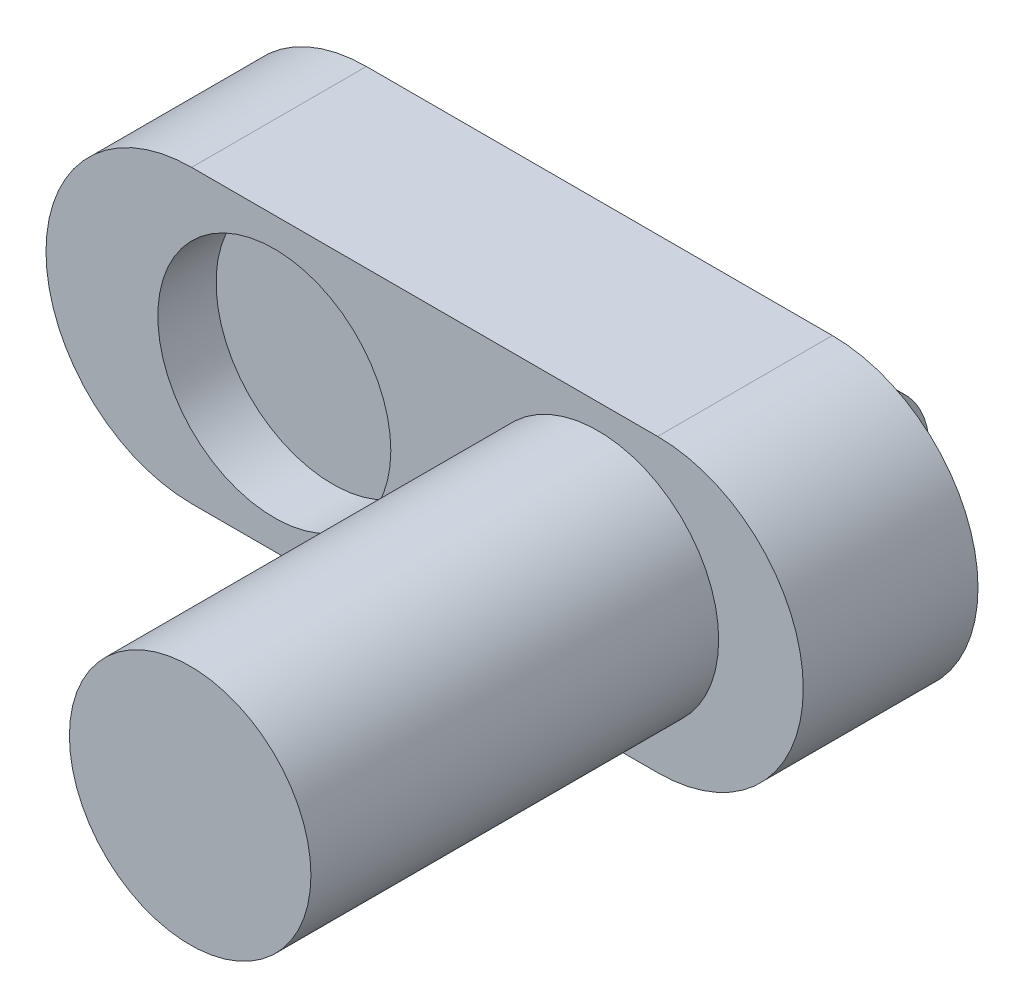
SolidWorks part; units mm, degrees
ref_plane "Front Plane" through (0, 0, 0) normal (0, 0, 1) x (1, 0, 0)
ref_plane "Top Plane" through (0, 0, 0) normal (0, 1, 0) x (1, 0, 0)
ref_plane "Right Plane" through (0, 0, 0) normal (1, 0, 0) x (0, 0, -1)
sketch "Sketch1" plane through (0, 0, 0) normal (0, 0, 1) x (1, 0, 0)
  line L0 (-20, 0) -> (20, 0) construction
  line L1 (-20, 12.5) -> (20, 12.5)
  line L2 (-20, -12.5) -> (20, -12.5)
  arc A0 (-20, 12.5) -> (-20, -12.5) centre (-20, 0) ccw
  arc A1 (20, -12.5) -> (20, 12.5) centre (20, 0) ccw
  point P2 (0, 0)
  dimension "D1" = 40
  dimension "D2" = 25
extrude "Boss-Extrude1" add sketch "Sketch1" along normal blind 5
sketch "Sketch2" plane through (0, 0, 5) normal (0, 0, 1) x (1, 0, 0)
  line L0 (-20, 0) -> (20, 0) construction
  line L1 (-20, 12.5) -> (20, 12.5)
  line L2 (-20, -12.5) -> (20, -12.5)
  arc A0 (-20, 12.5) -> (-20, -12.5) centre (-20, 0) ccw
  arc A1 (20, -12.5) -> (20, 12.5) centre (20, 0) ccw
  point P2 (0, 0)
  dimension "D1" = 40
  dimension "D2" = 25
extrude "Boss-Extrude2" add sketch "Sketch2" along normal blind 5
sketch "Sketch4" plane through (0, 0, 10) normal (0, 0, 1) x (1, 0, 0)
  line L0 (-20, 0) -> (20, 0) construction
  line L1 (-20, 12.5) -> (20, 12.5)
  line L2 (-20, -12.5) -> (20, -12.5)
  arc A0 (-20, 12.5) -> (-20, -12.5) centre (-20, 0) ccw
  arc A1 (20, -12.5) -> (20, 12.5) centre (20, 0) ccw
  point P2 (0, 0)
  dimension "D1" = 25
extrude "Boss-Extrude3" add sketch "Sketch4" along normal blind 5
sketch "Sketch5" plane through (0, 0, 15) normal (0, 0, 1) x (1, 0, 0)
  circle A0 centre (-12.902, 0) radius 7.5
  circle A1 centre (-12.902, 0) radius 10
  dimension "D1" = 20
  dimension "D2" = 15
extrude "Cut-Extrude1" cut sketch "Sketch5" against normal blind 5
sketch "Sketch6" plane through (0, 0, 15) normal (0, 0, 1) x (1, 0, 0)
  circle A0 centre (14.875, 0) radius 10.3661
extrude "Boss-Extrude4" add sketch "Sketch6" along normal blind 35
sketch "Sketch7" plane through (0, 0, 15) normal (0, 0, 1) x (1, 0, 0)
  circle A0 centre (-12.902, 0) radius 7.5
extrude "Cut-Extrude2" cut sketch "Sketch7" against normal blind 5
sketch "Sketch8" plane through (0, 0, 0) normal (0, 0, -1) x (-1, 0, 0)
  line L0 (32.5, 0) -> (-32.5, 0) construction
  line L1 (0, 12.5) -> (0, -12.5) construction
  line L2 (-20, 12.5) -> (20, 12.5) construction
  line L3 (20, -12.5) -> (-20, -12.5) construction
  line L4 (-20, 12.5) -> (-20, -12.5) construction
  line L5 (20, 12.5) -> (20, -12.5) construction
  arc A0 (20, -12.5) -> (20, 12.5) centre (20, 0) ccw construction
  arc A1 (-20, 12.5) -> (-20, -12.5) centre (-20, 0) ccw construction
  point P22 (0, 0)
ref_plane "Plane1" through (20, 0, 0) normal (1, 0, 0) x (0, 0, -1)
sketch "Sketch9" plane through (20, 0, 0) normal (1, 0, 0) x (0, 0, -1)
  line L0 (0, 6.25) -> (0, 0)
  line L1 (0, 0) -> (0, -6.25)
  line L2 (0, 6.25) -> (4.5, 6.25)
  line L4 (4.5, -6.25) -> (0, -6.25)
  arc A0 (4.5, 6.25) -> (4.5, -6.25) centre (1.2958, 0) cw
  point P0 (0, 0)
  point P4 (0, -6.25)
  point P7 (0, 6.25)
  dimension "D1" = 4.5
  dimension "D2" = 4.5
extrude "Boss-Extrude5" add sketch "Sketch9" against normal up to vertex (40 mm away) up to point (-20, -12.5, 0)
sketch "Sketch10" plane through (20, 0, 0) normal (1, 0, 0) x (0, 0, -1)
  line L0 (0, 0) -> (8.3193, 0) construction
  arc A0 (4.5, -6.25) -> (4.5, 6.25) centre (1.2958, 0) ccw construction
  circle A1 centre (4.1596, 0) radius 2.25
  point P6 (4.1596, 0)
  dimension "D1" = 4.5
extrude "Cut-Extrude3" cut sketch "Sketch10" against normal blind 40
